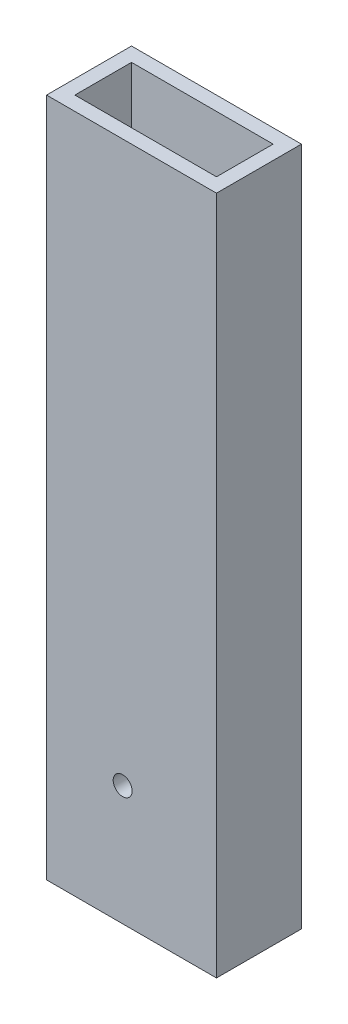
SolidWorks part; units mm, degrees
ref_plane "Front Plane" through (0, 0, 0) normal (0, 0, 1) x (1, 0, 0)
ref_plane "Top Plane" through (0, 0, 0) normal (0, 1, 0) x (1, 0, 0)
ref_plane "Right Plane" through (0, 0, 0) normal (1, 0, 0) x (0, 0, -1)
sketch "Sketch1" plane through (0, 0, 0) normal (0, 1, 0) x (1, 0, 0)
  line L0 (3.175, 15.875) -> (34.925, 15.875)
  line L1 (0, 0) -> (38.1, 0)
  line L2 (0, 0) -> (0, 19.05)
  line L3 (0, 19.05) -> (38.1, 19.05)
  line L4 (38.1, 0) -> (38.1, 19.05)
  line L5 (34.925, 3.175) -> (34.925, 15.875)
  line L6 (3.175, 3.175) -> (34.925, 3.175)
  line L7 (3.175, 3.175) -> (3.175, 15.875)
  dimension "D1" = 38.1
  dimension "D2" = 19.05
extrude "Boss-Extrude1" add sketch "Sketch1" along normal blind 152.4
sketch "Sketch2" plane through (0, 0, -19.05) normal (0, 0, -1) x (-1, 0, 0)
  circle A1 centre (-17.0622, 26.8327) radius 2.125
extrude "Cut-Extrude1" cut sketch "Sketch2" against normal through all
